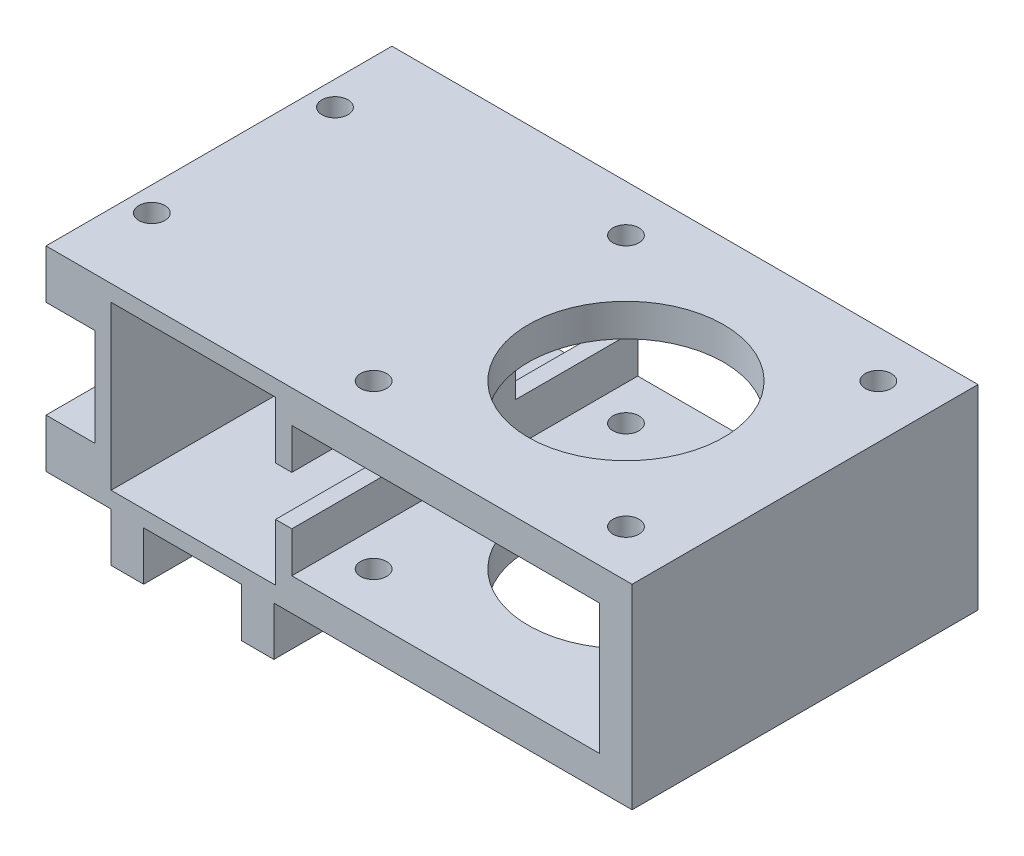
SolidWorks part; units mm, degrees
ref_plane "Plan de face" through (0, 0, 0) normal (0, 0, 1) x (1, 0, 0)
ref_plane "Plan de dessus" through (0, 0, 0) normal (0, 1, 0) x (1, 0, 0)
ref_plane "Plan de droite" through (0, 0, 0) normal (1, 0, 0) x (0, 0, -1)
sketch "Esquisse1" plane through (0, 0, 0) normal (0, 0, 1) x (1, 0, 0)
  line L0 (0, 0) -> (72, 0)
  line L1 (72, 0) -> (72, -24)
  line L2 (72, -24) -> (28, -24)
  line L3 (28, -24) -> (28, -30)
  line L4 (28, -30) -> (24, -30)
  line L5 (24, -30) -> (24, -24)
  line L6 (24, -24) -> (12, -24)
  line L7 (12, -24) -> (12, -30)
  line L8 (12, -30) -> (8, -30)
  line L9 (8, -30) -> (8, -24)
  line L10 (8, -24) -> (0, -24)
  line L11 (0, -24) -> (0, -18)
  line L12 (0, -18) -> (6, -18)
  line L13 (6, -18) -> (6, -6)
  line L14 (6, -6) -> (0, -6)
  line L15 (0, -6) -> (0, 0)
  line L17 (8, -2) -> (28.2, -2)
  line L18 (8, -2) -> (8, -22)
  line L19 (8, -22) -> (28.2, -22)
  line L20 (28.2, -2) -> (28.2, -22)
  line L21 (30.2, -4) -> (68, -4)
  line L22 (30.2, -4) -> (30.2, -20)
  line L23 (30.2, -20) -> (68, -20)
  line L24 (68, -4) -> (68, -20)
  dimension "D5" = 4
  dimension "D8" = 6
  dimension "D1" = 72
  dimension "D2" = 24
  dimension "D3" = 44
  dimension "D4" = 6
  dimension "D6" = 6
  dimension "D7" = 12
  dimension "D9" = 4
  dimension "D10" = 6
  dimension "D11" = 8
  dimension "D12" = 6
  dimension "D13" = 6
  dimension "D14" = 12
  dimension "D15" = 6
  dimension "D16" = 20.2
  dimension "D17" = 20
  dimension "D18" = 2
  dimension "D19" = 2
  dimension "D20" = 4
  dimension "D21" = 4
  dimension "D22" = 4
  dimension "D23" = 2
extrude "Boss.-Extru.1" add sketch "Esquisse1" along normal blind 42.5
sketch "Esquisse2" plane through (0, -24, 0) normal (0, -1, 0) x (1, 0, 0)
  line L0 (72, 21.25) -> (28, 21.25) construction
  line L1 (72, 42.5) -> (72, 0) construction
  line L2 (28, 42.5) -> (28, 0) construction
  circle A0 centre (50, 21.25) radius 12
  dimension "D1" = 24
  dimension "D2" = 22
extrude "Enlèv. mat.-Extru.1" cut sketch "Esquisse2" against normal through all
hole_wizard "Dégagement M31" positions "Esquisse4" profile "Esquisse3" hole size "M3" standard "Din" end condition through all
sketch "Esquisse4" plane through (0, -24, 0) normal (0, -1, 0) x (-1, 0, 0)
  line L1 (-65.5, -36.75) -> (-34.5, -36.75) construction
  line L2 (-65.5, -36.75) -> (-65.5, -5.75) construction
  line L3 (-65.5, -5.75) -> (-34.5, -5.75) construction
  line L4 (-34.5, -36.75) -> (-34.5, -5.75) construction
  line L5 (-65.5, -36.75) -> (-34.5, -5.75) construction
  line L6 (-65.5, -5.75) -> (-34.5, -36.75) construction
  point P1 (-50, -21.25)
  point P2 (-34.5, -5.75)
  point P5 (-65.5, -36.75)
  point P6 (-65.5, -5.75)
  point P7 (-34.5, -36.75)
  dimension "D1" = 31
  dimension "D2" = 31
sketch "Esquisse3" plane through (50, -24, 21.25) normal (1, 0, 0) x (0, 0, -1)
  line L0 (0, 0) -> (0, 24)
  line L1 (0, 24) -> (1.6, 24)
  line L2 (1.6, 24) -> (1.6, 0)
  line L5 (1.6, 0) -> (0, 0)
  line L11 (0, -6.35) -> (0, 107.95) construction
  dimension "Diamètre du perçage jusqu'au prochain" = 3.2
  dimension "Profondeur du perçage jusqu'au prochain" = 24
hole_wizard "Dégagement M32" positions "Esquisse6" profile "Esquisse7" hole size "M3" standard "Din" end condition through all
sketch "Esquisse6" plane through (28, 0, 0) normal (1, 0, 0) x (0, 0, -1)
  line L0 (-42.5, -27) -> (0, -27) construction
  line L1 (-42.5, -30) -> (-42.5, -24) construction
  line L2 (0, -30) -> (0, -24) construction
  point P0 (-10, -27)
  point P2 (-32.5, -27)
  dimension "D1" = 10
  dimension "D2" = 10
sketch "Esquisse7" plane through (28, -27, 10) normal (0, 1, 0) x (0, 0, -1)
  line L0 (0, 0) -> (0, 28)
  line L1 (0, 28) -> (1.6, 28)
  line L2 (1.6, 28) -> (1.6, 0)
  line L5 (1.6, 0) -> (0, 0)
  line L11 (0, -6.35) -> (0, 107.95) construction
  dimension "Diamètre du perçage jusqu'au prochain" = 3.2
  dimension "Profondeur du perçage jusqu'au prochain" = 28
hole_wizard "Dégagement M33" positions "Esquisse9" profile "Esquisse10" hole size "M3" standard "Din" end condition through all
sketch "Esquisse9" plane through (0, -24, 0) normal (0, -1, 0) x (-1, 0, 0)
  line L0 (-3, 0) -> (-3, -42.5) construction
  line L1 (0, 0) -> (-8, 0) construction
  line L2 (0, -42.5) -> (-8, -42.5) construction
  line L4 (0, -42.5) -> (0, 0) construction
  point P0 (-3, -10)
  point P2 (-3, -32.5)
  dimension "D1" = 10
  dimension "D2" = 10
  dimension "D3" = 3
sketch "Esquisse10" plane through (3, -24, 10) normal (1, 0, 0) x (0, 0, -1)
  line L0 (0, 0) -> (0, 24)
  line L1 (0, 24) -> (1.6, 24)
  line L2 (1.6, 24) -> (1.6, 0)
  line L5 (1.6, 0) -> (0, 0)
  line L11 (0, -6.35) -> (0, 107.95) construction
  dimension "Diamètre du perçage jusqu'au prochain" = 3.2
  dimension "Profondeur du perçage jusqu'au prochain" = 24
sketch "Esquisse11" plane through (30.2, 0, 0) normal (1, 0, 0) x (0, 0, -1)
  line L0 (0, -4) -> (0, -20) construction
  line L1 (0, -15) -> (-15, -15)
  line L2 (0, -15) -> (0, -9)
  line L3 (0, -9) -> (-15, -9)
  line L4 (-15, -15) -> (-15, -9)
  line L5 (-42.5, -4) -> (-42.5, -20) construction
  line L6 (-27.5, -15) -> (-42.5, -15)
  line L7 (-27.5, -15) -> (-27.5, -9)
  line L8 (-27.5, -9) -> (-42.5, -9)
  line L9 (-42.5, -15) -> (-42.5, -9)
  dimension "D1" = 15
  dimension "D2" = 15
  dimension "D3" = 6
  dimension "D4" = 5
extrude "Enlèv. mat.-Extru.2" cut sketch "Esquisse11" against normal up to next
